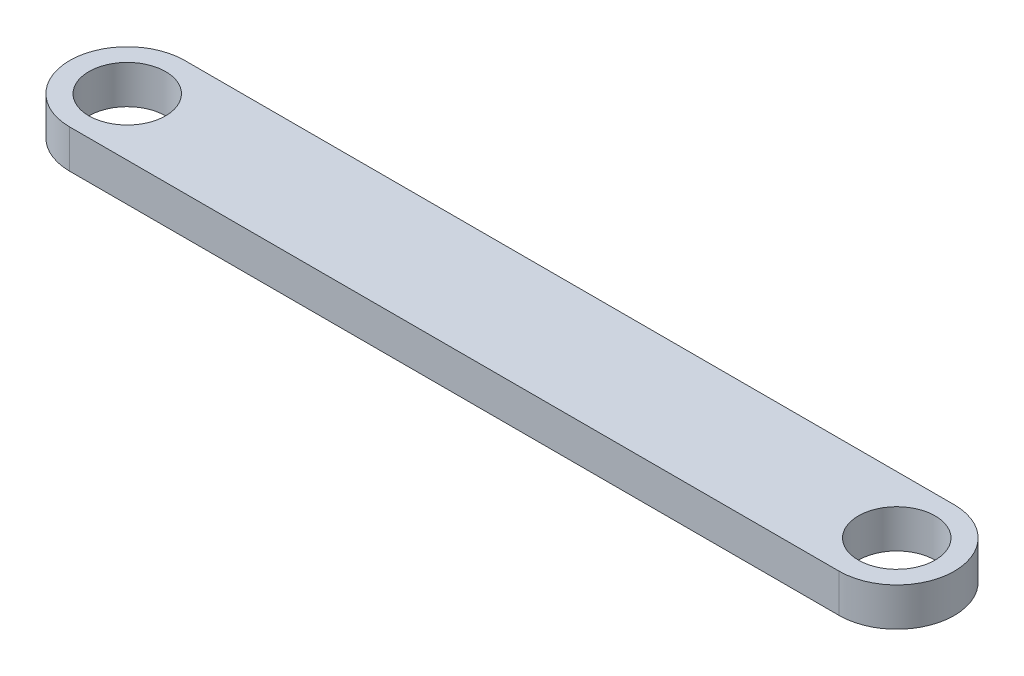
SolidWorks part; units mm, degrees
material "Thornel Mat VMA"
ref_plane "前视基准面" through (0, 0, 0) normal (0, 0, 1) x (1, 0, 0)
ref_plane "上视基准面" through (0, 0, 0) normal (0, 1, 0) x (1, 0, 0)
ref_plane "右视基准面" through (0, 0, 0) normal (1, 0, 0) x (0, 0, -1)
sketch "草图1" plane through (0, 0, 0) normal (0, 1, 0) x (1, 0, 0)
  line L0 (0, 0) -> (100.2809, 0) construction
  line L1 (0, 0) -> (99.7199, 7.479) construction
  line L2 (0, 7.5) -> (100.2809, 7.5)
  line L3 (0, -7.5) -> (100.2809, -7.5)
  line L4 (99.7199, 7.479) -> (100.2809, 0) construction
  arc A0 (0, 7.5) -> (0, -7.5) centre (0, 0) ccw
  arc A1 (100.2809, -7.5) -> (100.2809, 7.5) centre (100.2809, 0) ccw
  circle A2 centre (0, 0) radius 5
  circle A3 centre (100.2809, 0) radius 5
  point P5 (50.1404, 0)
  dimension "D2" = 7.5
  dimension "D3" = 10
  dimension "D4" = 7.5
  dimension "D1" = 100
extrude "凸台-拉伸1" add sketch "草图1" along normal blind 5
